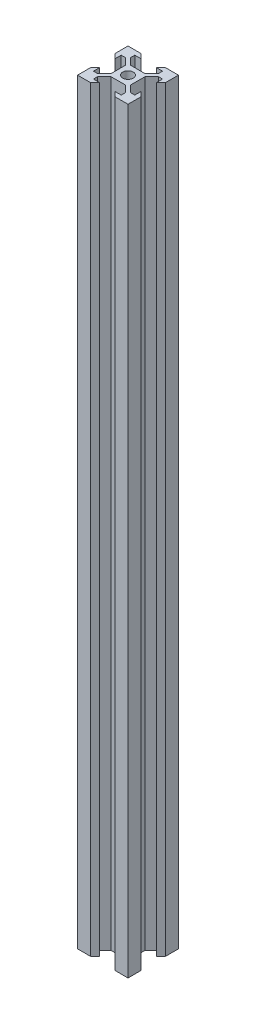
SolidWorks part; units mm, degrees
material "6061-T6 (SS)"
ref_plane "前视基准面" through (0, 0, 0) normal (0, 0, 1) x (1, 0, 0)
ref_plane "上视基准面" through (0, 0, 0) normal (0, 1, 0) x (1, 0, 0)
ref_plane "右视基准面" through (0, 0, 0) normal (1, 0, 0) x (0, 0, -1)
sketch "草图1" plane through (0, 0, 0) normal (0, 1, 0) x (1, 0, 0)
  line L0 (-10, 10) -> (-4.9, 10)
  line L1 (-10, -10) -> (10, -10) construction
  line L2 (-10, -10) -> (-10, 10) construction
  line L3 (-10, 10) -> (10, 10) construction
  line L4 (10, -10) -> (10, 10) construction
  line L5 (-10, -10) -> (10, 10) construction
  line L6 (-10, 10) -> (10, -10) construction
  line L7 (-4.9, 10) -> (-3.1, 8.2)
  line L8 (-3.1, 8.2) -> (-5.5, 8.2)
  line L9 (-5.5, 8.2) -> (-5.5, 6.5607)
  line L10 (-5.5, 6.5607) -> (-2.8393, 3.9)
  line L11 (-2.8393, 3.9) -> (0, 3.9)
  line L12 (0, 0) -> (0, 10) construction
  line L13 (-3.9, 2.8393) -> (-3.9, -2.8393)
  line L14 (-6.5607, 5.5) -> (-3.9, 2.8393)
  line L15 (-8.2, 5.5) -> (-6.5607, 5.5)
  line L16 (-8.2, 3.1) -> (-8.2, 5.5)
  line L17 (-10, 4.9) -> (-8.2, 3.1)
  line L18 (-10, 10) -> (-10, 4.9)
  line L19 (2.8393, 3.9) -> (0, 3.9)
  line L20 (10, 10) -> (10, 4.9)
  line L21 (10, 4.9) -> (8.2, 3.1)
  line L22 (8.2, 3.1) -> (8.2, 5.5)
  line L23 (8.2, 5.5) -> (6.5607, 5.5)
  line L24 (6.5607, 5.5) -> (3.9, 2.8393)
  line L25 (3.9, 2.8393) -> (3.9, -2.8393)
  line L26 (5.5, 6.5607) -> (2.8393, 3.9)
  line L27 (5.5, 8.2) -> (5.5, 6.5607)
  line L28 (3.1, 8.2) -> (5.5, 8.2)
  line L29 (4.9, 10) -> (3.1, 8.2)
  line L30 (10, 10) -> (4.9, 10)
  line L31 (-10, 0) -> (10, 0) construction
  line L32 (10, -10) -> (10, -4.9)
  line L33 (10, -10) -> (4.9, -10)
  line L34 (4.9, -10) -> (3.1, -8.2)
  line L35 (-4.9, -10) -> (-3.1, -8.2)
  line L36 (-10, -10) -> (-4.9, -10)
  line L37 (-10, -10) -> (-10, -4.9)
  line L38 (3.1, -8.2) -> (5.5, -8.2)
  line L39 (5.5, -8.2) -> (5.5, -6.5607)
  line L40 (5.5, -6.5607) -> (2.8393, -3.9)
  line L41 (6.5607, -5.5) -> (3.9, -2.8393)
  line L42 (8.2, -5.5) -> (6.5607, -5.5)
  line L43 (8.2, -3.1) -> (8.2, -5.5)
  line L44 (10, -4.9) -> (8.2, -3.1)
  line L45 (2.8393, -3.9) -> (0, -3.9)
  line L46 (-10, -4.9) -> (-8.2, -3.1)
  line L47 (-8.2, -3.1) -> (-8.2, -5.5)
  line L48 (-8.2, -5.5) -> (-6.5607, -5.5)
  line L49 (-6.5607, -5.5) -> (-3.9, -2.8393)
  line L50 (-2.8393, -3.9) -> (0, -3.9)
  line L51 (-5.5, -6.5607) -> (-2.8393, -3.9)
  line L52 (-5.5, -8.2) -> (-5.5, -6.5607)
  line L53 (-3.1, -8.2) -> (-5.5, -8.2)
  circle A0 centre (0, 0) radius 2.1
  point P0 (0, 0)
  point P23 (-1.4197, 3.9)
  point P24 (1.4197, 3.9)
  point P42 (-3.9, 0)
  point P43 (3.9, 0)
  point P56 (1.4197, -3.9)
  dimension "D9" = 4.2
  dimension "D1" = 20
  dimension "D2" = 20
  dimension "D3" = 0.75
  dimension "D4" = 1.8
  dimension "D5" = 4.9
  dimension "D6" = 3.1
  dimension "D7" = 5.5
  dimension "D8" = 6.1
extrude "凸台-拉伸1" add sketch "草图1" along normal blind 300
